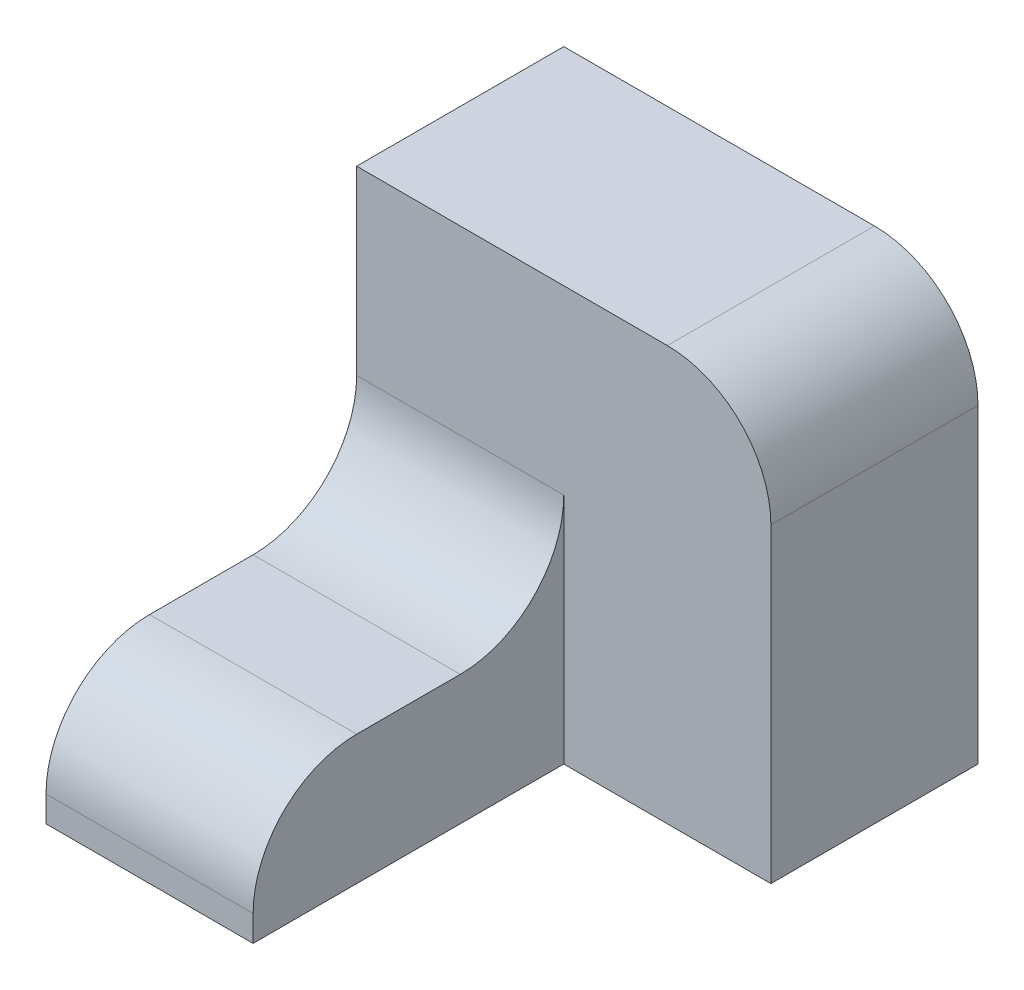
SolidWorks part; units mm, degrees
ref_plane "Front Plane" through (0, 0, 0) normal (0, 0, 1) x (1, 0, 0)
ref_plane "Top Plane" through (0, 0, 0) normal (0, 1, 0) x (1, 0, 0)
ref_plane "Right Plane" through (0, 0, 0) normal (1, 0, 0) x (0, 0, -1)
sketch "Sketch1" plane through (0, 0, 0) normal (0, 0, 1) x (1, 0, 0)
  line L1 (-30, -12.5) -> (-10, -12.5)
  line L2 (-10, -12.5) -> (-10, 0)
  line L3 (-10, 0) -> (-30, 0)
  line L4 (-30, 0) -> (-30, -12.5)
  dimension "D1" = 20
  dimension "Width" = 12.5
extrude "Boss-Extrude1" add sketch "Sketch1" along normal blind 30
sketch "Sketch2" plane through (0, 0, 0) normal (0, 0, 1) x (1, 0, 0)
  line L1 (-30, -12.5) -> (10, -12.5)
  line L2 (10, -12.5) -> (10, 27.5)
  line L3 (10, 27.5) -> (-30, 27.5)
  line L4 (-30, 27.5) -> (-30, -12.5)
  dimension "D1" = 40
  dimension "Width" = 40
extrude "Boss-Extrude2" add sketch "Sketch2" against normal blind 20
fillet "Fillet1" radius 10 3 edges at (-20, 0, 0) (10, 27.5, -10) (-20, 0, 30)
